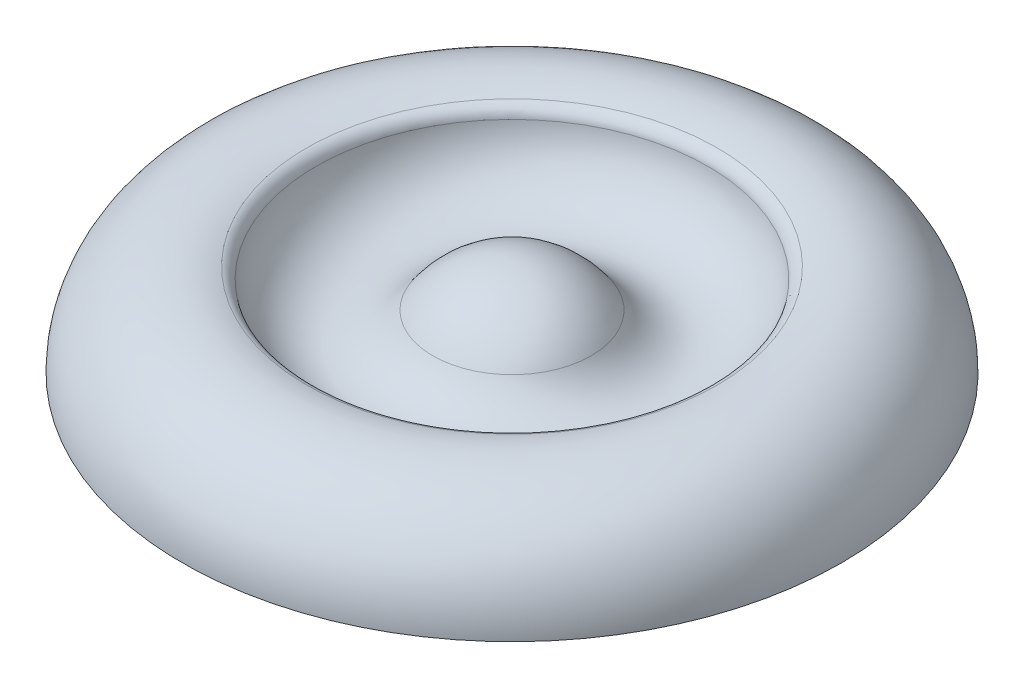
SolidWorks part; units mm, degrees
ref_plane "Front Plane" through (0, 0, 0) normal (0, 0, 1) x (1, 0, 0)
ref_plane "Top Plane" through (0, 0, 0) normal (0, 1, 0) x (1, 0, 0)
ref_plane "Right Plane" through (0, 0, 0) normal (1, 0, 0) x (0, 0, -1)
sketch "Sketch1" plane through (0, 0, 0) normal (0, 0, 1) x (1, 0, 0)
  line L0 (0, 0) -> (76.2, 0)
  line L1 (0, 0) -> (0, 22.2034)
  arc A0 (76.2, 0) -> (47.4882, 21.2573) centre (53.975, 0) ccw
  arc A1 (18.3249, 12.5375) -> (0, 22.2034) centre (0, 0) ccw
  arc A2 (18.3249, 12.5375) -> (45.2758, 18.697) centre (30.5869, 20.9269) ccw
  arc A3 (47.4882, 21.2573) -> (45.2758, 18.697) centre (48.4149, 18.2205) ccw
  point P2 (53.975, 0)
  dimension "D3" = 3.175
  dimension "D1" = 76.2
  dimension "D2" = 22.225
revolve "Revolve1" add sketch "Sketch1" angle 360 about L1
